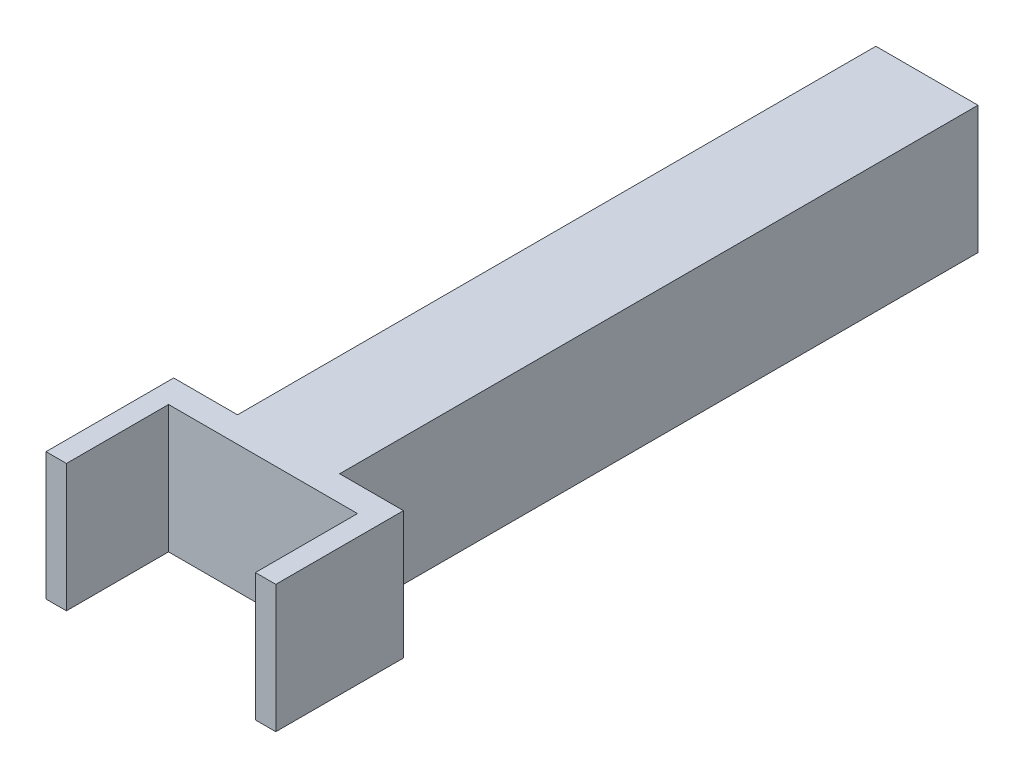
SolidWorks part; units mm, degrees
ref_plane "Płaszczyzna przednia" through (0, 0, 0) normal (0, 0, 1) x (1, 0, 0)
ref_plane "Płaszczyzna górna" through (0, 0, 0) normal (0, 1, 0) x (1, 0, 0)
ref_plane "Płaszczyzna prawa" through (0, 0, 0) normal (1, 0, 0) x (0, 0, -1)
sketch "Szkic1" plane through (0, 0, 0) normal (0, 0, 1) x (1, 0, 0)
  line L1 (20, 25) -> (-20, 25)
  line L2 (20, 25) -> (20, -25)
  line L3 (20, -25) -> (-20, -25)
  line L4 (-20, 25) -> (-20, -25)
  line L5 (20, 25) -> (-20, -25) construction
  line L6 (20, -25) -> (-20, 25) construction
  point P0 (0, 0)
  dimension "D1" = 40
  dimension "D2" = 50
extrude "Dodanie-wyciągnięcie1" add sketch "Szkic1" along normal blind 250
sketch "Szkic2" plane through (0, 0, 250) normal (0, 0, 1) x (1, 0, 0)
  line L1 (45, 25) -> (-45, 25)
  line L2 (45, 25) -> (45, -25)
  line L3 (45, -25) -> (-45, -25)
  line L4 (-45, 25) -> (-45, -25)
  line L5 (45, 25) -> (-45, -25) construction
  line L6 (45, -25) -> (-45, 25) construction
  point P0 (0, 0)
  dimension "D1" = 90
extrude "Dodanie-wyciągnięcie2" add sketch "Szkic2" along normal blind 10
sketch "Szkic3" plane through (0, 0, 260) normal (0, 0, 1) x (1, 0, 0)
  line L0 (0, 38.2527) -> (0, -38.2527) construction
  line L1 (-45, -25) -> (45, -25) construction
  line L2 (-45, 25) -> (-37, 25)
  line L3 (-45, 25) -> (-45, -25)
  line L4 (-45, -25) -> (-37, -25)
  line L5 (-37, 25) -> (-37, -25)
  line L6 (37, 25) -> (37, -25)
  line L7 (45, -25) -> (37, -25)
  line L8 (45, 25) -> (45, -25)
  line L9 (45, 25) -> (37, 25)
  point P4 (0, 0)
  dimension "D1" = 8
extrude "Dodanie-wyciągnięcie3" add sketch "Szkic3" along normal blind 40
